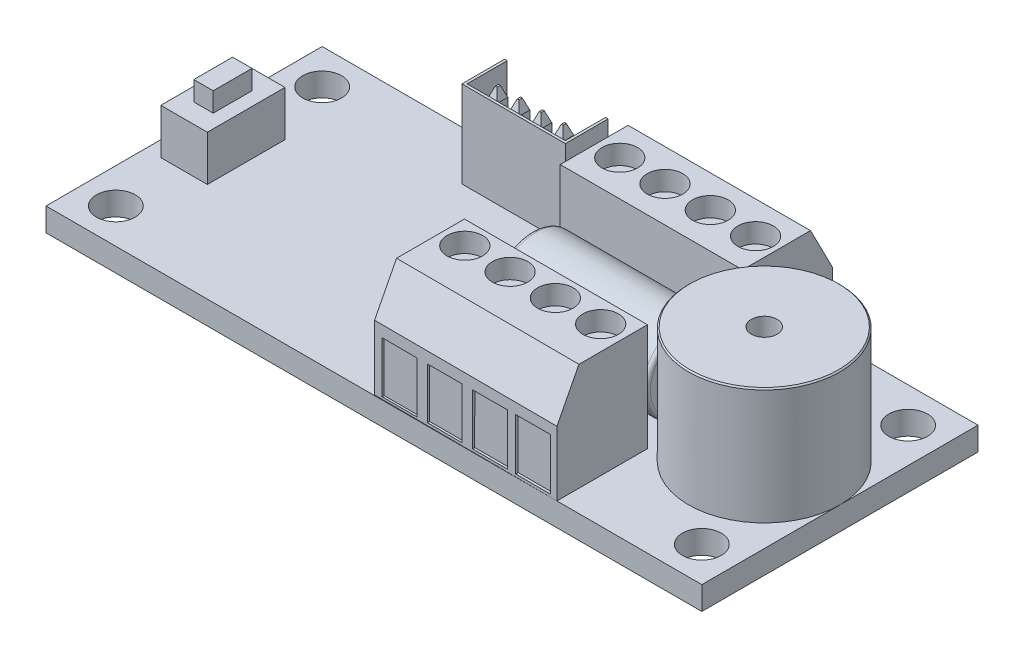
SolidWorks part; units mm, degrees
ref_plane "Front" through (0, 0, 0) normal (0, 0, 1) x (1, 0, 0)
ref_plane "Top" through (0, 0, 0) normal (0, 1, 0) x (1, 0, 0)
ref_plane "Right" through (0, 0, 0) normal (1, 0, 0) x (0, 0, -1)
sketch "Sketch1" plane through (0, 0, 0) normal (0, 1, 0) x (1, 0, 0)
  line L1 (-22.561, 10.3591) -> (28.139, 10.3591)
  line L2 (-22.561, 10.3591) -> (-22.561, -10.9909)
  line L3 (-22.561, -10.9909) -> (28.139, -10.9909)
  line L4 (28.139, 10.3591) -> (28.139, -10.9909)
  circle A0 centre (-19.861, 7.6591) radius 1.5
  circle A1 centre (-19.861, -8.2909) radius 1.5
  circle A2 centre (25.439, 7.6591) radius 1.5
  circle A3 centre (25.439, -8.2909) radius 1.5
  dimension "D3" = 2.7
  dimension "D5" = 2.7
  dimension "D7" = 2.7
  dimension "D9" = 3
  dimension "D1" = 50.7
  dimension "D2" = 21.35
  dimension "D4" = 2.7
  dimension "D6" = 2.7
  dimension "D8" = 2.7
  dimension "D10" = 2.7
  dimension "D11" = 2.7
extrude "Boss-Extrude1" add sketch "Sketch1" along normal blind 1.8
sketch "Sketch2" plane through (0, 1.8, 0) normal (0, 1, 0) x (1, 0, 0)
  line L0 (28.139, -10.9909) -> (28.139, 10.3591) construction
  line L3 (-22.561, -10.9909) -> (28.139, -10.9909) construction
  line L4 (28.139, 10.3591) -> (-22.561, 10.3591) construction
  circle A0 centre (22.289, -0.3159) radius 5.85
  point P2 (11.627, -3.9327)
  point P5 (28.139, -0.3159)
  dimension "D1" = 11.7
  dimension "D2" = 5.85
  dimension "D3" = 0
extrude "Boss-Extrude2" add sketch "Sketch2" along normal blind 9
sketch "Sketch3" plane through (0, 10.8, 0) normal (0, 1, 0) x (1, 0, 0)
  circle A0 centre (22.289, -0.3159) radius 1
extrude "Cut-Extrude1" cut sketch "Sketch3" against normal blind 8
chamfer "Chamfer1" distance 0.1 angle 45 1 edges at (22.289, 10.8, 6.1659)
ref_plane "Plane1" through (16.439, 0, 0) normal (-1, 0, 0) x (0, 0, 1)
sketch "Sketch4" plane through (16.439, 0, 0) normal (-1, 0, 0) x (0, 0, 1)
  line L0 (6.1659, 1.8) -> (-5.5341, 1.8) construction
  line L1 (10.9909, 1.8) -> (10.9909, 0) construction
  circle A0 centre (0.3109, 5.05) radius 3.25
  dimension "D1" = 6.5
  dimension "D2" = 3.25
  dimension "D3" = 10.68
extrude "Boss-Extrude3" add sketch "Sketch4" along normal blind 12.1 separate body
fillet "Fillet1" radius 0.3 1 edges at (16.439, 5.05, 3.5609)
fillet "Fillet2" radius 0.3 1 edges at (4.339, 5.05, 3.5609)
sketch "Sketch5" plane through (0, 1.8, 0) normal (0, 1, 0) x (1, 0, 0)
  line L0 (-22.561, 10.3591) -> (-22.561, -10.9909) construction
  line L1 (-21.361, 2.6841) -> (-17.761, 2.6841)
  line L2 (-21.361, 2.6841) -> (-21.361, -3.3159)
  line L3 (-21.361, -3.3159) -> (-17.761, -3.3159)
  line L4 (-17.761, 2.6841) -> (-17.761, -3.3159)
  point P6 (-21.361, -0.3159)
  point P7 (-22.561, -0.3159)
  dimension "D1" = 3.6
  dimension "D2" = 6
  dimension "D3" = 1.2
  dimension "D4" = 0
extrude "Boss-Extrude4" add sketch "Sketch5" along normal blind 3.5 contours L2 L3 L4 L1
sketch "Sketch6" plane through (0, 5.3, 0) normal (0, 1, 0) x (1, 0, 0)
  line L0 (-21.361, 2.6841) -> (-21.361, -3.3159) construction
  line L1 (-18.811, 1.1841) -> (-20.311, 1.1841)
  line L2 (-18.811, 1.1841) -> (-18.811, -1.8159)
  line L3 (-18.811, -1.8159) -> (-20.311, -1.8159)
  line L4 (-20.311, 1.1841) -> (-20.311, -1.8159)
  line L5 (-18.811, 1.1841) -> (-20.311, -1.8159) construction
  line L6 (-18.811, -1.8159) -> (-20.311, 1.1841) construction
  line L7 (-21.361, 2.6841) -> (-17.761, 2.6841) construction
  point P0 (-19.561, -0.3159)
  point P5 (-20.311, -0.3159)
  point P8 (-21.361, -0.3159)
  point P9 (-19.561, 1.1841)
  point P12 (-19.561, 2.6841)
  dimension "D1" = 3
  dimension "D2" = 1.5
  dimension "D3" = 0
  dimension "D4" = 0
extrude "Boss-Extrude5" add sketch "Sketch6" along normal blind 1.5
sketch "Sketch7" plane through (0, 1.8, 0) normal (0, 1, 0) x (1, 0, 0)
  line L0 (28.139, 10.3591) -> (-22.561, 10.3591) construction
  line L1 (16.939, 3.3591) -> (2.839, 3.3591)
  line L2 (16.939, 3.3591) -> (16.939, 10.3091)
  line L3 (16.939, 10.3091) -> (2.839, 10.3091)
  line L4 (2.839, 3.3591) -> (2.839, 10.3091)
  line L6 (28.139, -0.3159) -> (28.139, 10.3591) construction
  line L7 (-22.561, -10.9909) -> (28.139, -10.9909) construction
  line L8 (16.939, -10.9909) -> (2.789, -10.9409)
  line L9 (16.939, -10.9909) -> (16.939, -3.9909)
  line L10 (16.939, -3.9909) -> (2.789, -3.9909)
  line L11 (2.789, -10.9409) -> (2.789, -3.9909)
  line M14 (28.139, 10.3591) -> (-22.561, 10.3591)
  dimension "D1" = 14.1
  dimension "D2" = 6.95
  dimension "D4" = 11.2
  dimension "D5" = 6.95
  dimension "D6" = 7
  dimension "D7" = 7
extrude "Boss-Extrude6" add sketch "Sketch7" along normal blind 8.3 contours L4 L1 L2 M14 | L9 L10 L11 L8
chamfer "Chamfer2" distance 3.3 distance2 1.7 1 edges at (9.889, 10.1, -10.3091)
chamfer "Chamfer3" distance 1.7 distance2 3.3 1 edges at (9.864, 10.1, 10.9659)
sketch "Sketch8" plane through (0, 0, -10.3591) normal (0, 0, -1) x (-1, 0, 0)
  line L1 (-16.439, 6.3) -> (-13.739, 6.3)
  line L2 (-16.439, 6.3) -> (-16.439, 2.3)
  line L3 (-16.439, 2.3) -> (-13.739, 2.3)
  line L4 (-13.739, 6.3) -> (-13.739, 2.3)
  line L6 (-12.939, 6.3) -> (-12.939, 2.3)
  line L7 (-10.239, 6.3) -> (-10.239, 2.3)
  line L8 (-12.939, 6.3) -> (-10.239, 6.3)
  line L9 (-12.939, 2.3) -> (-10.239, 2.3)
  line L10 (-9.439, 6.3) -> (-9.439, 2.3)
  line L11 (-6.739, 6.3) -> (-6.739, 2.3)
  line L12 (-9.439, 6.3) -> (-6.739, 6.3)
  line L13 (-9.439, 2.3) -> (-6.739, 2.3)
  line L14 (-5.939, 6.3) -> (-5.939, 2.3)
  line L15 (-3.239, 6.3) -> (-3.239, 2.3)
  line L16 (-5.939, 6.3) -> (-3.239, 6.3)
  line L17 (-5.939, 2.3) -> (-3.239, 2.3)
  dimension "D3" = 4
  dimension "D4" = 2.7
  dimension "D5" = 4
extrude "Cut-Extrude2" cut sketch "Sketch8" against normal blind 0.2
sketch "Sketch9" plane through (0, 10.1, 0) normal (0, 1, 0) x (1, 0, 0)
  line L0 (16.939, 3.3591) -> (16.939, 8.6091) construction
  circle A0 centre (15.189, 6.1154) radius 1.375
  circle A1 centre (11.689, 6.1154) radius 1.375
  circle A2 centre (8.189, 6.1154) radius 1.375
  circle A3 centre (4.689, 6.1154) radius 1.375
  dimension "D1" = 1.75
  dimension "D2" = 4
extrude "Cut-Extrude3" cut sketch "Sketch9" against normal blind 1.5
sketch "Sketch10" plane through (0, 10.1, 0) normal (0, 1, 0) x (1, 0, 0)
  line L1 (16.939, -10.9909) -> (16.939, -3.9909) construction
  circle A0 centre (15.089, -5.7617) radius 1.375
  circle A1 centre (11.589, -5.7617) radius 1.375
  circle A2 centre (8.089, -5.7617) radius 1.375
  circle A3 centre (4.589, -5.7617) radius 1.375
  dimension "D1" = 1.85
  dimension "D2" = 4
extrude "Cut-Extrude4" cut sketch "Sketch10" against normal blind 1.5 contours A0 | A2 | A3 | A1
sketch "Sketch11" plane through (0, 0, 10.9909) normal (0, 0, 1) x (1, 0, 0)
  line L0 (3.3848, 5.9255) -> (6.0848, 5.9255)
  line L1 (3.3848, 5.9255) -> (3.3848, 1.9755)
  line L2 (3.3848, 1.9755) -> (6.0848, 1.9755)
  line L3 (6.0848, 5.9255) -> (6.0848, 1.9755)
  line L4 (6.8846, 5.931) -> (6.8842, 2)
  line L5 (9.5845, 5.9495) -> (9.5842, 2)
  line L6 (6.8846, 5.931) -> (9.5845, 5.9495)
  line L7 (6.8842, 2) -> (9.5842, 2)
  line L8 (10.3845, 5.955) -> (10.3842, 2)
  line L9 (13.0843, 5.9735) -> (13.0842, 2)
  line L10 (10.3845, 5.955) -> (13.0843, 5.9735)
  line L11 (10.3842, 2) -> (13.0842, 2)
  line L12 (13.7391, 5.978) -> (13.739, 2)
  line L13 (16.439, 5.9966) -> (16.439, 2)
  line L14 (13.7391, 5.978) -> (16.439, 5.9966)
  line L15 (13.739, 2) -> (16.439, 2)
  line L16 (16.939, 6.8) -> (16.939, 1.8) construction
  line L17 (16.939, 6.8) -> (2.789, 6.7029) construction
  line L18 (16.939, 6.8) -> (2.789, 6.8) construction
  dimension "D1" = 3.95
  dimension "D2" = 2.7
  dimension "D3" = 0.5
  dimension "D4" = 0.8
  dimension "D5" = 0.8
  dimension "D6" = 0.8
  dimension "D7" = 3.9495
  dimension "D8" = 0.8745
extrude "Cut-Extrude5" cut sketch "Sketch11" against normal blind 0.2 contours L4 L7 L5 L6 | L8 L11 L9 L10 | L12 L15 L13 L14 | L0 L3 L2 L1
sketch "Sketch13" plane through (0, 1.8, 0) normal (0, 1, 0) x (1, 0, 0)
  line L0 (2.839, 3.3591) -> (2.839, 10.3091) construction
  line L1 (-7.961, 9.8591) -> (0.039, 9.8591)
  line L2 (-7.961, 9.8591) -> (-7.961, 6.5591)
  line L3 (-7.961, 6.5591) -> (0.039, 6.5591)
  line L4 (0.039, 9.8591) -> (0.039, 6.5591)
  line L5 (28.139, 10.3591) -> (-22.561, 10.3591) construction
  point P6 (2.839, 6.8341)
  dimension "D1" = 8
  dimension "D2" = 3.3
  dimension "D3" = 2.8
  dimension "D4" = 0.5
extrude "Boss-Extrude7" add sketch "Sketch13" along normal blind 2.7
sketch "Sketch14" plane through (0, 4.5, 0) normal (0, 1, 0) x (1, 0, 0)
  line L0 (-0.161, 9.8591) -> (0.039, 9.8591)
  line L1 (-7.961, 9.8591) -> (-7.761, 9.8591)
  line L2 (-7.961, 9.8591) -> (-7.961, 6.5591)
  line L3 (-7.961, 6.5591) -> (0.039, 6.5591)
  line L4 (0.039, 9.8591) -> (0.039, 6.5591)
  line L5 (-5.1086, 7.4144) -> (-4.3832, 8.2352) construction
  line L6 (-7.761, 9.8591) -> (-7.761, 6.7591)
  line L7 (-7.761, 6.7591) -> (-0.161, 6.7591)
  line L8 (-0.161, 9.8591) -> (-0.161, 6.7591)
  line L9 (-6.8086, 7.4144) -> (-6.0832, 7.4144)
  line L10 (-6.8086, 7.4144) -> (-6.8086, 8.2352)
  line L11 (-6.8086, 8.2352) -> (-6.0832, 8.2352)
  line L12 (-6.0832, 7.4144) -> (-6.0832, 8.2352)
  line L13 (-6.8086, 7.4144) -> (-6.0832, 8.2352) construction
  line L14 (-6.8086, 8.2352) -> (-6.0832, 7.4144) construction
  line L15 (-5.1086, 8.2352) -> (-4.3832, 7.4144) construction
  line L16 (-5.1086, 7.4144) -> (-5.1086, 8.2352)
  line L17 (-5.1086, 7.4144) -> (-4.3832, 7.4144)
  line L18 (-4.3832, 7.4144) -> (-4.3832, 8.2352)
  line L19 (-5.1086, 8.2352) -> (-4.3832, 8.2352)
  line L20 (-3.4086, 7.4144) -> (-2.6832, 8.2352) construction
  line L21 (-3.4086, 8.2352) -> (-2.6832, 7.4144) construction
  line L22 (-3.4086, 7.4144) -> (-3.4086, 8.2352)
  line L23 (-3.4086, 7.4144) -> (-2.6832, 7.4144)
  line L24 (-2.6832, 7.4144) -> (-2.6832, 8.2352)
  line L25 (-3.4086, 8.2352) -> (-2.6832, 8.2352)
  line L26 (-1.7086, 7.4144) -> (-0.9832, 8.2352) construction
  line L27 (-1.7086, 8.2352) -> (-0.9832, 7.4144) construction
  line L28 (-1.7086, 7.4144) -> (-1.7086, 8.2352)
  line L29 (-1.7086, 7.4144) -> (-0.9832, 7.4144)
  line L30 (-0.9832, 7.4144) -> (-0.9832, 8.2352)
  line L31 (-1.7086, 8.2352) -> (-0.9832, 8.2352)
  point P10 (-6.4459, 7.8248)
  point P16 (-4.7459, 7.8248)
  point P21 (-3.0459, 7.8248)
  point P26 (-1.3459, 7.8248)
  dimension "D1" = 0.2
  dimension "D2" = 0.2
  dimension "D3" = 0.2
  dimension "D4" = 4
extrude "Boss-Extrude8" add sketch "Sketch14" along normal blind 4
chamfer "Chamfer4" distance 0.8 angle 20 16 edges at (-0.9832, 8.5, -7.8248) (-1.3459, 8.5, -7.4144) (-1.7086, 8.5, -7.8248) (-1.3459, 8.5, -8.2352) (-2.6832, 8.5, -7.8248) (-3.0459, 8.5, -7.4144) (-3.4086, 8.5, -7.8248) (-3.0459, 8.5, -8.2352) (-4.3832, 8.5, -7.8248) (-4.7459, 8.5, -7.4144) (-5.1086, 8.5, -7.8248) (-4.7459, 8.5, -8.2352) (-6.4459, 8.5, -7.4144) (-6.8086, 8.5, -7.8248) (-6.4459, 8.5, -8.2352) (-6.0832, 8.5, -7.8248)
